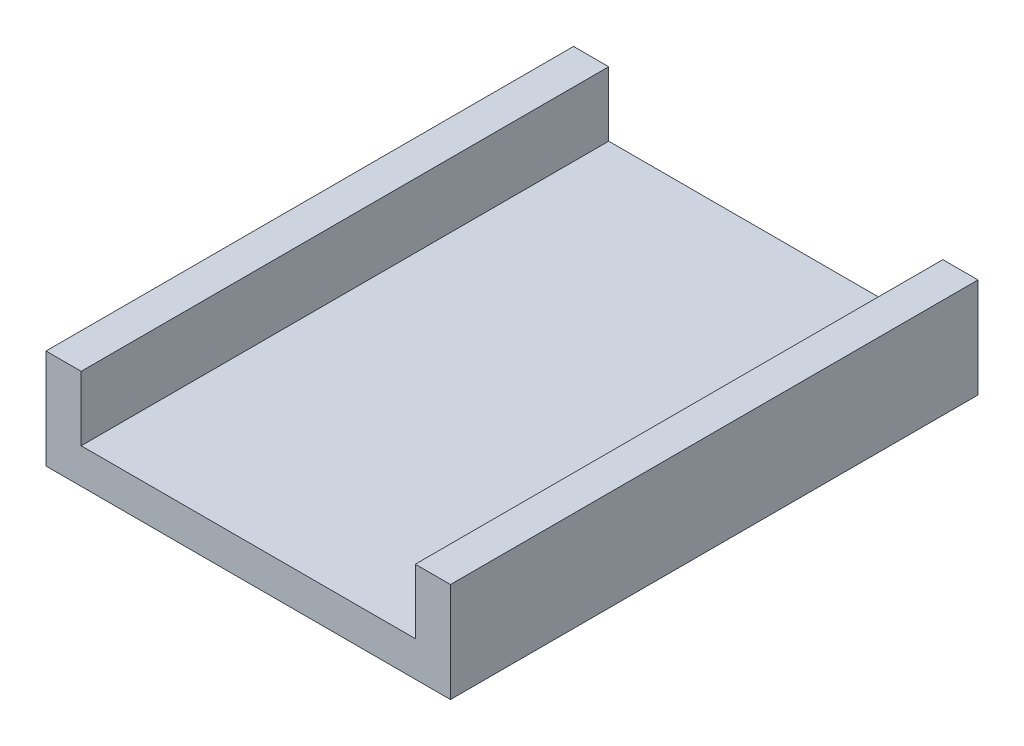
SolidWorks part; units mm, degrees
material "Custom Plastic"
ref_plane "Front Plane" through (0, 0, 0) normal (0, 0, 1) x (1, 0, 0)
ref_plane "Top Plane" through (0, 0, 0) normal (0, 1, 0) x (1, 0, 0)
ref_plane "Right Plane" through (0, 0, 0) normal (1, 0, 0) x (0, 0, -1)
sketch "Sketch2" plane through (0, 0, 0) normal (0, 1, 0) x (1, 0, 0)
  line L1 (-17.25, -22.5) -> (17.25, -22.5)
  line L2 (-17.25, -22.5) -> (-17.25, 22.5)
  line L3 (-17.25, 22.5) -> (17.25, 22.5)
  line L4 (17.25, -22.5) -> (17.25, 22.5)
  line L5 (-17.25, -22.5) -> (17.25, 22.5) construction
  line L6 (-17.25, 22.5) -> (17.25, -22.5) construction
  point P0 (0, 0)
  dimension "D1" = 34.5
  dimension "D2" = 45
extrude "Boss-Extrude1" add sketch "Sketch2" along normal blind 3
sketch "Sketch3" plane through (0, 3, 0) normal (0, 1, 0) x (1, 0, 0)
  line L0 (-14.25, 22.5) -> (-14.25, -22.5)
  line L1 (17.25, 22.5) -> (-17.25, 22.5) construction
  line L2 (-17.25, -22.5) -> (17.25, -22.5) construction
  line L3 (14.25, 22.5) -> (14.25, -22.5)
  line L4 (17.25, -22.5) -> (17.25, 22.5) construction
  line L5 (-17.25, 22.5) -> (-17.25, -22.5) construction
  line L6 (-14.25, 22.5) -> (-17.25, 22.5)
  line L7 (-17.25, 22.5) -> (-17.25, -22.5)
  line L8 (-17.25, -22.5) -> (-14.25, -22.5)
  line L9 (14.25, 22.5) -> (17.25, 22.5)
  line L10 (17.25, 22.5) -> (17.25, -22.5)
  line L11 (17.25, -22.5) -> (14.25, -22.5)
  dimension "D1" = 3
  dimension "D2" = 3
extrude "Boss-Extrude2" add sketch "Sketch3" along normal blind 5.5
